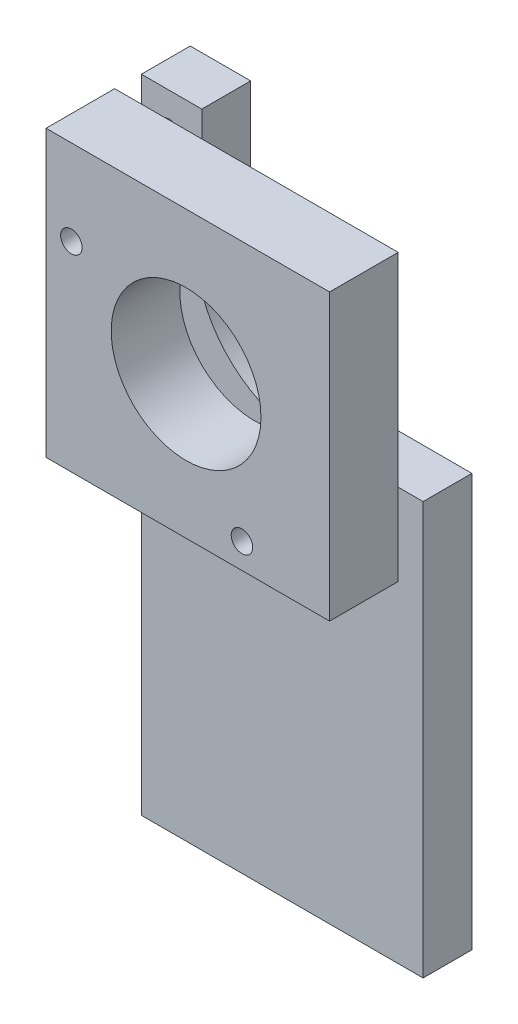
SolidWorks part; units mm, degrees
ref_plane "Front Plane" through (0, 0, 0) normal (0, 0, 1) x (1, 0, 0)
ref_plane "Top Plane" through (0, 0, 0) normal (0, 1, 0) x (1, 0, 0)
ref_plane "Right Plane" through (0, 0, 0) normal (1, 0, 0) x (0, 0, -1)
sketch "Sketch1" plane through (0, 0, 0) normal (0, 0, 1) x (1, 0, 0)
  line L1 (0, 0) -> (32.86, 0)
  line L2 (0, 0) -> (0, 33.04)
  line L3 (0, 33.04) -> (32.86, 33.04)
  line L4 (32.86, 0) -> (32.86, 33.04)
  circle A0 centre (16.23, 16.48) radius 8.68
  circle A1 centre (2.935, 23.145) radius 1.245
  circle A2 centre (22.705, 2.935) radius 1.245
  dimension "D3" = 17.36
  dimension "D5" = 16.23
  dimension "D6" = 2.49
  dimension "D7" = 2.935
  dimension "D9" = 2.49
  dimension "D10" = 2.935
  dimension "D1" = 32.86
  dimension "D2" = 33.04
  dimension "D4" = 16.48
  dimension "D8" = 9.895
  dimension "D11" = 22.705
extrude "Boss-Extrude1" add sketch "Sketch1" along normal blind 7.95
sketch "Sketch2" plane through (0, 0, 0) normal (0, 0, -1) x (-1, 0, 0)
  circle A0 centre (-3.3058, 28.8634) radius 1.2718
extrude "Boss-Extrude2" add sketch "Sketch2" along normal blind 3
sketch "Sketch3" plane through (0, 0, -3) normal (0, 0, -1) x (-1, 0, 0)
  line L0 (0, 33.04) -> (0, 0) construction
  line L1 (-0.1, 33.04) -> (-7.1, 33.04)
  line L2 (-0.1, 33.04) -> (-0.1, -41.35)
  line L3 (-0.1, -41.35) -> (-32.75, -41.35)
  line L4 (-32.75, 6.47) -> (-32.75, -41.35)
  line L5 (-32.86, 33.04) -> (0, 33.04) construction
  line L6 (-7.1, 33.04) -> (-7.1, 23.04)
  line L7 (-32.75, 6.47) -> (-23.75, 6.47)
  arc A0 (-23.75, 6.47) -> (-7.1, 23.04) centre (-19.4964, 18.846) ccw
  dimension "D9" = 13.0866
  dimension "D1" = 74.39
  dimension "D2" = 32.65
  dimension "D3" = 0.1
  dimension "D4" = 0
  dimension "D5" = 7
  dimension "D6" = 10
  dimension "D7" = 26.57
  dimension "D8" = 9
extrude "Boss-Extrude3" add sketch "Sketch3" along normal blind 5.66
